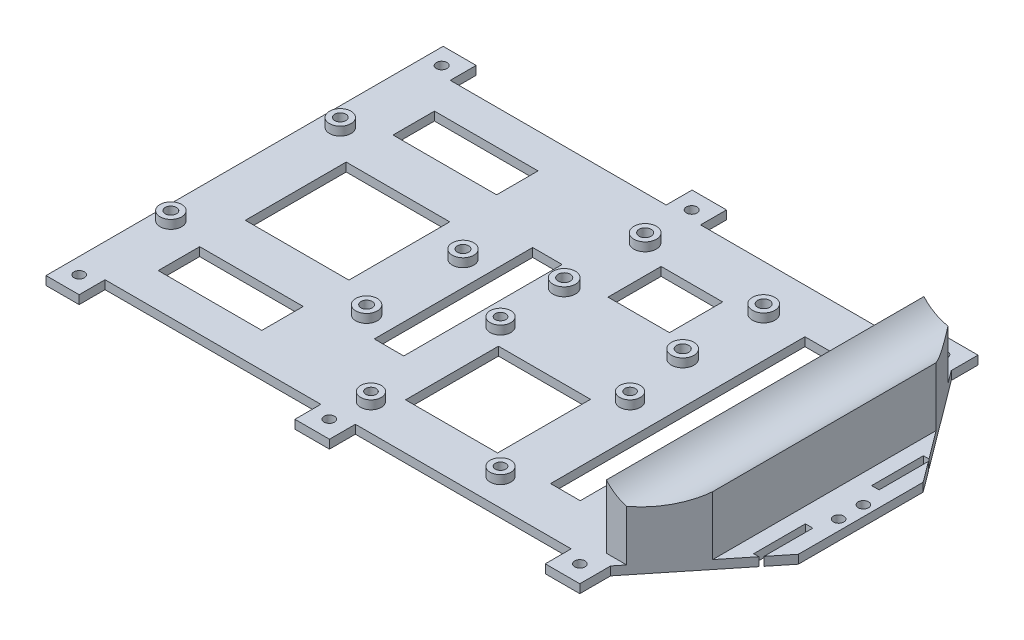
SolidWorks part; units mm, degrees
ref_plane "Front Plane" through (0, 0, 0) normal (0, 0, 1) x (1, 0, 0)
ref_plane "Top Plane" through (0, 0, 0) normal (0, 1, 0) x (1, 0, 0)
ref_plane "Right Plane" through (0, 0, 0) normal (1, 0, 0) x (0, 0, -1)
sketch "Sketch1" plane through (-134.9624, -12.3323, 36.871) normal (0, 1, 0) x (1, 0, 0)
  circle A0 centre (14.0144, 2.7114) radius 1.6192 construction
  circle A1 centre (14.0144, 2.7114) radius 3.1192
  circle A2 centre (15.1574, 50.6285) radius 1.6192 construction
  circle A3 centre (65.9447, 35.3885) radius 1.6193 construction
  circle A4 centre (65.9447, 7.4612) radius 1.6193 construction
  circle A5 centre (15.1574, 50.6285) radius 1.6192
  circle A6 centre (65.9447, 35.3885) radius 1.6193
  circle A7 centre (65.9447, 7.4612) radius 1.6193
  circle A8 centre (14.0144, 2.7114) radius 1.6192
  circle A9 centre (65.9447, 7.4612) radius 3.1193
  circle A10 centre (65.9447, 35.3885) radius 3.1193
  circle A11 centre (15.1574, 50.6285) radius 3.1192
  dimension "D1" = 1.5
ref_plane "Plane1" through (0, -17.3323, 0) normal (0, -1, 0) x (-1, 0, 0)
sketch "Sketch2" plane through (0, -17.3323, 0) normal (0, -1, 0) x (-1, 0, 0)
  line L0 (-29.353, -57.1027) -> (-29.6746, 41.2342) construction
  line L4 (125.2416, -58.531) -> (125.2416, 41.469)
  line L5 (-29.6746, 41.2342) -> (-53.6103, 9.1478)
  line L7 (125.2416, 41.469) -> (125.2416, 48.9753)
  line L8 (125.2416, 48.9753) -> (115.6688, 48.9753)
  line L9 (115.6688, 41.469) -> (115.6688, 48.9753)
  line L11 (53.1359, 41.469) -> (53.1359, 48.9753)
  line L12 (53.1359, 48.9753) -> (43.1688, 48.9753)
  line L13 (43.1688, 41.469) -> (43.1688, 48.9753)
  line L15 (-19.2544, 41.469) -> (-19.2544, 48.9753)
  line L16 (-19.2544, 48.9753) -> (-29.6746, 48.9753)
  line L17 (-29.6746, 41.2342) -> (-29.6746, 48.9753)
  line L19 (-19.353, -58.531) -> (-19.353, -66.0361)
  line L20 (-19.353, -66.0361) -> (-29.353, -66.0361)
  line L21 (-29.353, -57.1027) -> (-29.353, -66.0361)
  line L22 (-29.353, -57.1027) -> (-53.6103, -26.9752)
  line L24 (53.147, -58.531) -> (53.147, -66.0361)
  line L25 (53.147, -66.0361) -> (43.147, -66.0361)
  line L26 (43.147, -58.531) -> (43.147, -66.0361)
  line L27 (53.147, -58.531) -> (115.647, -58.531)
  line L29 (125.2416, -58.531) -> (125.2416, -66.0361)
  line L30 (125.2416, -66.0361) -> (115.647, -66.0361)
  line L31 (115.647, -58.531) -> (115.647, -66.0361)
  line L32 (-19.353, -58.531) -> (43.147, -58.531)
  line L33 (-19.2544, 41.469) -> (43.1688, 41.469)
  line L34 (53.1359, 41.469) -> (115.6688, 41.469)
  line L37 (-53.6103, -26.9752) -> (-53.6103, 9.1478)
extrude "Boss-Extrude1" add sketch "Sketch2" against normal blind 2.5
extrude "Boss-Extrude2" add sketch "Sketch1" against normal up to surface (2.5 mm away) up to face at (-33.1593, -14.8323, 8.5129)
sketch "Sketch12" plane through (0, -14.8323, 0) normal (0, 1, 0) x (1, 0, 0)
  circle A0 centre (-119.8049, 13.7575) radius 1.6192
  circle A1 centre (-69.0176, -1.4825) radius 1.6193
  circle A2 centre (-69.0176, -29.4098) radius 1.6193
  circle A3 centre (-120.9479, -34.1596) radius 1.6193
extrude "Cut-Extrude2" cut sketch "Sketch12" against normal through all
sketch "Sketch13" plane through (0, -14.8323, 0) normal (0, 1, 0) x (1, 0, 0)
  circle A0 centre (-46.6207, -13.0221) radius 1.5
  circle A1 centre (-9.1028, -13.0221) radius 1.5
  circle A2 centre (-46.6207, -50.54) radius 1.5
  circle A3 centre (-9.1028, -50.54) radius 1.5
sketch "Sketch15" plane through (0, -14.8323, 0) normal (0, 1, 0) x (1, 0, 0)
  circle A16 centre (-46.6207, -50.54) radius 3
  circle A17 centre (-46.6207, -50.54) radius 3
  circle A19 centre (-46.6207, -13.0221) radius 3
  circle A20 centre (-46.6207, -13.0221) radius 3
  circle A22 centre (-9.1028, -50.54) radius 3
  circle A23 centre (-9.1028, -50.54) radius 3
  circle A25 centre (-9.1028, -13.0221) radius 3
  circle A26 centre (-9.1028, -13.0221) radius 3
  dimension "D1" = 1.5
  dimension "D2" = 1.5
  dimension "D3" = 1.5
  dimension "D4" = 1.5
extrude "Boss-Extrude6" add sketch "Sketch15" along normal blind 2.5
extrude "Cut-Extrude5" cut sketch "Sketch13" against normal through all both and the other way through all
sketch "Sketch16" plane through (0, -14.8323, 0) normal (0, 1, 0) x (1, 0, 0)
  circle A0 centre (-46.7265, 28.969) radius 1.75
  circle A1 centre (-47.1666, 5.9732) radius 1.7551
  circle A2 centre (-12.173, 5.3035) radius 1.7551
  circle A3 centre (-11.7329, 28.2993) radius 1.75
  circle A4 centre (-11.7329, 28.2993) radius 3.25
  circle A5 centre (-12.173, 5.3035) radius 3.2551
  circle A6 centre (-47.1666, 5.9732) radius 3.2551
  circle A7 centre (-46.7265, 28.969) radius 3.25
  dimension "D1" = 1.5
extrude "Boss-Extrude7" add sketch "Sketch16" along normal blind 2.5 contours A5 | A4 | A7 | A6
sketch "Sketch17" plane through (0, -12.3323, 0) normal (0, 1, 0) x (1, 0, 0)
  circle A0 centre (-46.7265, 28.969) radius 1.75
  circle A1 centre (-47.1666, 5.9732) radius 1.7551
  circle A2 centre (-12.173, 5.3035) radius 1.7551
  circle A3 centre (-11.7329, 28.2993) radius 1.75
extrude "Cut-Extrude6" cut sketch "Sketch17" against normal through all both and the other way through all
sketch "Sketch24" plane through (0, -14.8323, 0) normal (0, 1, 0) x (1, 0, 0)
  circle A0 centre (-120.6315, 43.9363) radius 1.5346
  circle A1 centre (-48.1932, 43.9363) radius 1.5397
  circle A2 centre (24.3749, 43.9363) radius 1.5351
  circle A3 centre (24.3749, -61.0358) radius 1.5073
  circle A4 centre (-48.1932, -61.0358) radius 1.5018
  circle A5 centre (-120.6315, -61.0358) radius 1.5067
extrude "Cut-Extrude7" cut sketch "Sketch24" against normal through all both and the other way through all
sketch "Sketch25" plane through (0, -14.8323, 0) normal (0, 1, 0) x (1, 0, 0)
  line L0 (25.5244, 37.469) -> (32.4834, 37.469)
  line L5 (25.5244, 37.469) -> (25.5244, -54.531)
  line L6 (25.5244, -54.531) -> (31.4236, -54.531)
  line L7 (42.5443, 23.9821) -> (42.5443, -40.7192)
  line L8 (31.4236, -54.531) -> (42.5443, -40.7192)
  line L9 (19.353, -58.531) -> (-43.147, -58.531) construction
  line L11 (19.2544, 41.469) -> (-43.1688, 41.469) construction
  line L12 (29.353, -57.1027) -> (53.6103, -26.9752) construction
  line L13 (32.4834, 37.469) -> (42.5443, 23.9821)
  line L14 (29.6746, 41.2342) -> (53.6103, 9.1478) construction
  dimension "D1" = 4
  dimension "D2" = 4
extrude "Boss-Extrude8" add sketch "Sketch25" along normal blind 23
sketch "Sketch28" plane through (0, -14.8323, 0) normal (0, 1, 0) x (1, 0, 0)
  line L15 (20.6854, -33.3294) -> (22.596, -33.3294)
  line L20 (20.6854, -33.3294) -> (20.6854, -18.3294)
  line L21 (20.6854, -18.3294) -> (22.596, -18.3294)
  line L22 (22.596, -33.3294) -> (22.596, -18.3294)
  line L23 (20.6854, 0.8385) -> (22.596, 0.8385)
  line L24 (20.6854, 0.8385) -> (20.6854, 15.8385)
  line L25 (20.6854, 15.8385) -> (22.596, 15.8385)
  line L26 (22.596, 0.8385) -> (22.596, 15.8385)
  line L27 (46.996, -33.3294) -> (49.157, -33.3294)
  line L28 (46.996, -33.3294) -> (46.996, -18.3294)
  line L29 (46.996, -18.3294) -> (49.157, -18.3294)
  line L30 (49.157, -33.3294) -> (49.157, -18.3294)
  line L31 (46.996, 0.8385) -> (49.157, 0.8385)
  line L32 (46.996, 0.8385) -> (46.996, 15.8385)
  line L33 (46.996, 15.8385) -> (49.157, 15.8385)
  line L34 (49.157, 0.8385) -> (49.157, 15.8385)
extrude "Cut-Extrude9" cut sketch "Sketch28" against normal through all
sketch "Sketch29" plane through (0, 0, 16.4516) normal (0, 0, -1) x (-1, 0, 0)
  circle A0 centre (-34.7234, 11.702) radius 12.2 construction
  circle A1 centre (-34.7234, 11.702) radius 12.2 construction
  circle A2 centre (-34.7234, 11.702) radius 12.3
  dimension "D1" = 0.1
sketch "Sketch30" plane through (0, -14.8323, 0) normal (0, 1, 0) x (1, 0, 0)
  line L0 (-125.2416, -58.531) -> (-125.2416, 41.469) construction
  line L1 (-110.2416, -36.531) -> (-80.2416, -36.531)
  line L2 (-110.2416, -36.531) -> (-110.2416, -48.531)
  line L3 (-110.2416, -48.531) -> (-80.2416, -48.531)
  line L4 (-80.2416, -36.531) -> (-80.2416, -48.531)
  line L5 (-110.2416, 31.469) -> (-80.2416, 31.469)
  line L6 (-110.2416, 31.469) -> (-110.2416, 19.469)
  line L7 (-110.2416, 19.469) -> (-80.2416, 19.469)
  line L8 (-80.2416, 31.469) -> (-80.2416, 19.469)
  line L9 (-53.1359, 41.469) -> (-115.6688, 41.469) construction
  line L10 (-53.147, -58.531) -> (-115.647, -58.531) construction
  line L12 (-61.8108, -34.3983) -> (-53.2676, -34.3983)
  line L13 (-61.8108, -34.3983) -> (-61.8108, 11.4767)
  line L14 (-61.8108, 11.4767) -> (-53.2676, 11.4767)
  line L15 (-53.2676, -34.3983) -> (-53.2676, 11.4767)
  line L16 (-110.2416, -23.3098) -> (-80.2416, -23.3098)
  line L17 (-110.2416, -23.3098) -> (-110.2416, 5.9065)
  line L18 (-110.2416, 5.9065) -> (-80.2416, 5.9065)
  line L19 (-80.2416, -23.3098) -> (-80.2416, 5.9065)
  line L20 (-42.0102, -45.1416) -> (-15.3454, -45.1416)
  line L21 (-42.0102, -45.1416) -> (-42.0102, -18.2192)
  line L22 (-42.0102, -18.2192) -> (-15.3454, -18.2192)
  line L23 (-15.3454, -45.1416) -> (-15.3454, -18.2192)
  line L24 (-38.4568, 9.9316) -> (-20.6382, 9.9316)
  line L25 (-38.4568, 9.9316) -> (-38.4568, 25.3337)
  line L26 (-38.4568, 25.3337) -> (-20.6382, 25.3337)
  line L27 (-20.6382, 9.9316) -> (-20.6382, 25.3337)
  line L28 (0, -45.1416) -> (8.5919, -45.1416)
  line L29 (0, -45.1416) -> (0, 28.5298)
  line L30 (0, 28.5298) -> (8.5919, 28.5298)
  line L31 (8.5919, -45.1416) -> (8.5919, 28.5298)
  point P8 (-80.2416, 25.469)
  dimension "D1" = 30
  dimension "D2" = 12
  dimension "D3" = 12
  dimension "D4" = 30
  dimension "D5" = 15
  dimension "D6" = 15
  dimension "D7" = 10
  dimension "D8" = 10
extrude "Cut-Extrude11" cut sketch "Sketch30" against normal through all
extrude "Cut-Extrude12" cut sketch "Sketch29" against normal through all both and the other way through all
sketch "Sketch31" plane through (0, -14.8323, 0) normal (0, 1, 0) x (1, 0, 0)
  line L0 (53.6103, 9.1478) -> (53.6103, -26.9752) construction
  line L1 (46.996, 0.8385) -> (49.157, 0.8385) construction
  line L2 (49.157, -18.3294) -> (46.996, -18.3294) construction
  circle A0 centre (50.6103, -12.3294) radius 1.5
  circle A1 centre (50.6103, -5.1615) radius 1.5
  dimension "D1" = 3
  dimension "D2" = 3
  dimension "D3" = 3
  dimension "D4" = 3
  dimension "D5" = 6
  dimension "D6" = 6
extrude "Cut-Extrude13" cut sketch "Sketch31" against normal through all both and the other way through all
sketch "Sketch32" plane through (0, -17.3323, 0) normal (0, -1, 0) x (1, 0, 0)
  line L0 (30.5244, 47.6751) -> (30.5244, -31.7329)
  line L1 (30.5244, -31.7329) -> (30.5244, -31.7329)
  line L2 (30.5244, -31.7329) -> (37.5443, -22.3226)
  line L3 (37.5443, -22.3226) -> (37.5443, 38.9565)
  line L4 (37.5443, 38.9565) -> (30.5244, 47.6751)
  line L5 (30.5244, 47.6751) -> (30.5244, 47.6751)
  line L6 (25.5244, -37.469) -> (32.4834, -37.469)
  line L7 (32.4834, -37.469) -> (42.5443, -23.9821)
  line L8 (42.5443, -23.9821) -> (42.5443, 40.7192)
  line L9 (42.5443, 40.7192) -> (31.4236, 54.531)
  line L10 (31.4236, 54.531) -> (25.5244, 54.531)
  line L11 (25.5244, 54.531) -> (25.5244, -37.469)
  line L12 (25.5244, -37.469) -> (32.4834, -37.469) construction
  line L13 (32.4834, -37.469) -> (42.5443, -23.9821) construction
  line L14 (42.5443, -23.9821) -> (42.5443, 40.7192) construction
  line L15 (42.5443, 40.7192) -> (31.4236, 54.531) construction
  line L16 (31.4236, 54.531) -> (25.5244, 54.531) construction
  line L17 (25.5244, 54.531) -> (25.5244, -37.469) construction
  dimension "D1" = 0
  dimension "D2" = 5
extrude "Cut-Extrude14" cut sketch "Sketch32" against normal blind 12
